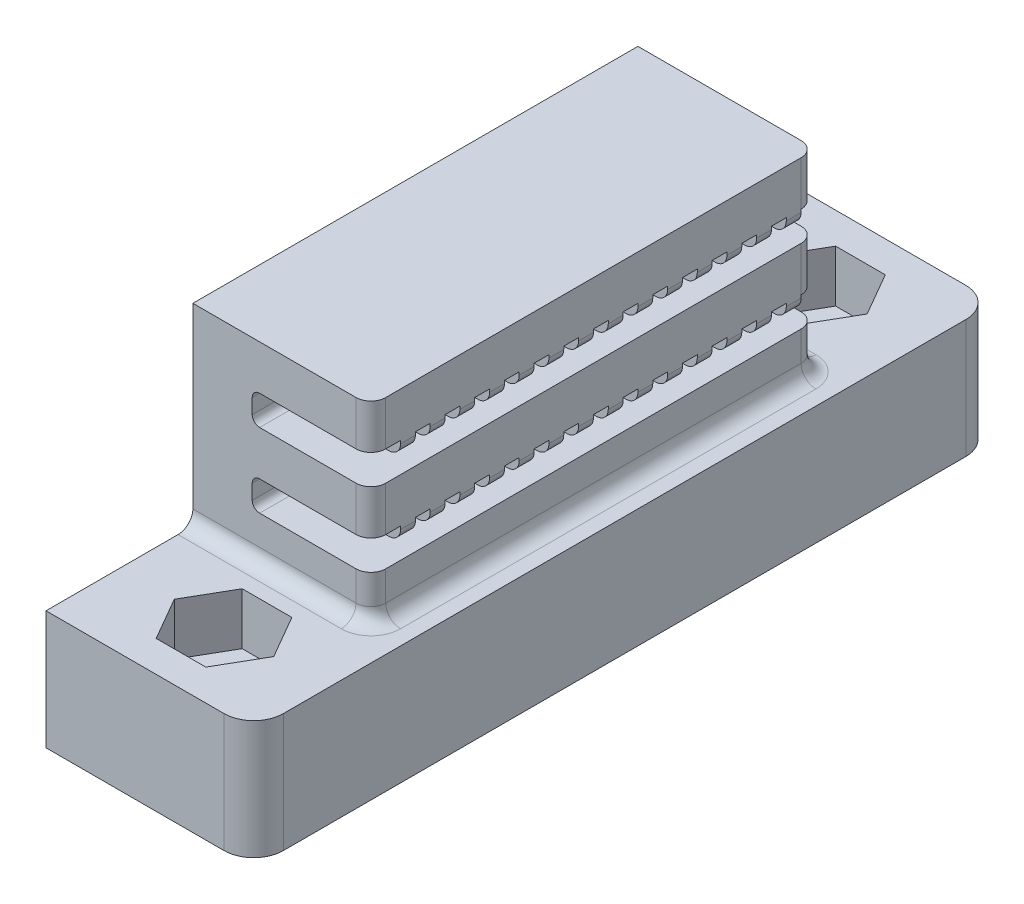
SolidWorks part; units mm, degrees
ref_plane "Alzado" through (0, 0, 0) normal (0, 0, 1) x (1, 0, 0)
ref_plane "Planta" through (0, 0, 0) normal (0, 1, 0) x (1, 0, 0)
ref_plane "Vista lateral" through (0, 0, 0) normal (1, 0, 0) x (0, 0, -1)
sketch "Croquis1" plane through (0, 0, 0) normal (0, 1, 0) x (1, 0, 0)
  line L0 (0, 25) -> (14, 25) construction
  line L1 (0, 0) -> (14, 0)
  line L2 (0, 0) -> (0, 50)
  line L3 (0, 50) -> (14, 50)
  line L4 (14, 0) -> (14, 50)
  line L5 (7, 50) -> (7, 0) construction
  circle A0 centre (7, 45) radius 1.55
  circle A1 centre (7, 5) radius 1.55
  dimension "D3" = 3.1
  dimension "D1" = 50
  dimension "D2" = 14
  dimension "D4" = 20
extrude "Saliente-Extruir1" add sketch "Croquis1" along normal blind 8
sketch "Croquis2" plane through (0, 8, 0) normal (0, 1, 0) x (1, 0, 0)
  line L1 (10.3486, 45) -> (8.6743, 47.9)
  line L2 (8.6743, 47.9) -> (5.3257, 47.9)
  line L3 (5.3257, 47.9) -> (3.6514, 45)
  line L4 (3.6514, 45) -> (5.3257, 42.1)
  line L5 (5.3257, 42.1) -> (8.6743, 42.1)
  line L6 (8.6743, 42.1) -> (10.3486, 45)
  line L7 (10.3486, 5) -> (8.6743, 7.9)
  line L8 (8.6743, 7.9) -> (5.3257, 7.9)
  line L9 (5.3257, 7.9) -> (3.6514, 5)
  line L10 (3.6514, 5) -> (5.3257, 2.1)
  line L11 (5.3257, 2.1) -> (8.6743, 2.1)
  line L12 (8.6743, 2.1) -> (10.3486, 5)
  circle A2 centre (7, 45) radius 2.9 construction
  circle A3 centre (7, 5) radius 2.9 construction
  dimension "D1" = 5.8
  dimension "D2" = 5.8
extrude "Cortar-Extruir1" cut sketch "Croquis2" against normal blind 3.5
sketch "Croquis3" plane through (0, 8, 0) normal (0, 1, 0) x (1, 0, 0)
  line L0 (0, 50) -> (0, 0) construction
  line L1 (0, 39.9) -> (14, 39.9)
  line L2 (0, 39.9) -> (0, 9.9)
  line L3 (0, 9.9) -> (14, 9.9)
  line L4 (14, 39.9) -> (14, 9.9)
  line L5 (14, 0) -> (14, 50) construction
  line L6 (5.3257, 42.1) -> (8.6743, 42.1) construction
  dimension "D1" = 30
  dimension "D2" = 2.2
extrude "Saliente-Extruir3" add sketch "Croquis3" along normal blind 13
sketch "Croquis4" plane through (14, 0, 0) normal (1, 0, 0) x (0, 0, -1)
  line L0 (39.9, 21) -> (39.9, 8) construction
  line L1 (39.9, 18) -> (38.9, 18)
  line L2 (39.9, 18) -> (39.9, 16)
  line L3 (39.9, 16) -> (9.9, 16)
  line L4 (9.9, 18) -> (9.9, 16)
  line L5 (9.9, 21) -> (9.9, 8) construction
  line L6 (39.9, 8) -> (50, 8) construction
  line L7 (39.9, 13) -> (38.9, 13)
  line L8 (39.9, 13) -> (39.9, 11)
  line L9 (39.9, 11) -> (9.9, 11)
  line L10 (9.9, 13) -> (9.9, 11)
  line L11 (36.9, 18) -> (36.9, 17)
  line L13 (38.9, 18) -> (38.9, 17)
  line L14 (38.9, 17) -> (37.9, 17)
  line L15 (37.9, 18) -> (37.9, 17)
  line L16 (36.9, 17) -> (35.9, 17)
  line L17 (35.9, 18) -> (35.9, 17)
  line L18 (34.9, 18) -> (34.9, 17)
  line L19 (34.9, 17) -> (33.9, 17)
  line L20 (33.9, 18) -> (33.9, 17)
  line L21 (32.9, 18) -> (32.9, 17)
  line L22 (32.9, 17) -> (31.9, 17)
  line L23 (31.9, 18) -> (31.9, 17)
  line L24 (30.9, 18) -> (30.9, 17)
  line L25 (30.9, 17) -> (29.9, 17)
  line L26 (29.9, 18) -> (29.9, 17)
  line L27 (28.9, 18) -> (28.9, 17)
  line L28 (28.9, 17) -> (27.9, 17)
  line L29 (27.9, 18) -> (27.9, 17)
  line L30 (26.9, 18) -> (26.9, 17)
  line L31 (26.9, 17) -> (25.9, 17)
  line L32 (25.9, 18) -> (25.9, 17)
  line L33 (24.9, 18) -> (24.9, 17)
  line L34 (24.9, 17) -> (23.9, 17)
  line L35 (23.9, 18) -> (23.9, 17)
  line L36 (22.9, 18) -> (22.9, 17)
  line L37 (22.9, 17) -> (21.9, 17)
  line L38 (21.9, 18) -> (21.9, 17)
  line L39 (20.9, 18) -> (20.9, 17)
  line L40 (20.9, 17) -> (19.9, 17)
  line L41 (19.9, 18) -> (19.9, 17)
  line L42 (18.9, 18) -> (18.9, 17)
  line L43 (18.9, 17) -> (17.9, 17)
  line L44 (17.9, 18) -> (17.9, 17)
  line L45 (16.9, 18) -> (16.9, 17)
  line L46 (16.9, 17) -> (15.9, 17)
  line L47 (15.9, 18) -> (15.9, 17)
  line L48 (14.9, 18) -> (14.9, 17)
  line L49 (14.9, 17) -> (13.9, 17)
  line L50 (13.9, 18) -> (13.9, 17)
  line L51 (12.9, 18) -> (12.9, 17)
  line L52 (12.9, 17) -> (11.9, 17)
  line L53 (11.9, 18) -> (11.9, 17)
  line L54 (38.9, 18) -> (36.9, 18) construction
  line L55 (36.9, 13) -> (36.9, 12)
  line L57 (38.9, 13) -> (38.9, 12)
  line L58 (38.9, 12) -> (37.9, 12)
  line L59 (37.9, 13) -> (37.9, 12)
  line L60 (36.9, 12) -> (35.9, 12)
  line L61 (35.9, 13) -> (35.9, 12)
  line L62 (34.9, 13) -> (34.9, 12)
  line L63 (34.9, 12) -> (33.9, 12)
  line L64 (33.9, 13) -> (33.9, 12)
  line L65 (32.9, 13) -> (32.9, 12)
  line L66 (32.9, 12) -> (31.9, 12)
  line L67 (31.9, 13) -> (31.9, 12)
  line L68 (30.9, 13) -> (30.9, 12)
  line L69 (30.9, 12) -> (29.9, 12)
  line L70 (29.9, 13) -> (29.9, 12)
  line L71 (28.9, 13) -> (28.9, 12)
  line L72 (28.9, 12) -> (27.9, 12)
  line L73 (27.9, 13) -> (27.9, 12)
  line L74 (26.9, 13) -> (26.9, 12)
  line L75 (26.9, 12) -> (25.9, 12)
  line L76 (25.9, 13) -> (25.9, 12)
  line L77 (24.9, 13) -> (24.9, 12)
  line L78 (24.9, 12) -> (23.9, 12)
  line L79 (23.9, 13) -> (23.9, 12)
  line L80 (22.9, 13) -> (22.9, 12)
  line L81 (22.9, 12) -> (21.9, 12)
  line L82 (21.9, 13) -> (21.9, 12)
  line L83 (20.9, 13) -> (20.9, 12)
  line L84 (20.9, 12) -> (19.9, 12)
  line L85 (19.9, 13) -> (19.9, 12)
  line L86 (18.9, 13) -> (18.9, 12)
  line L87 (18.9, 12) -> (17.9, 12)
  line L88 (17.9, 13) -> (17.9, 12)
  line L89 (16.9, 13) -> (16.9, 12)
  line L90 (16.9, 12) -> (15.9, 12)
  line L91 (15.9, 13) -> (15.9, 12)
  line L92 (14.9, 13) -> (14.9, 12)
  line L93 (14.9, 12) -> (13.9, 12)
  line L94 (13.9, 13) -> (13.9, 12)
  line L95 (12.9, 13) -> (12.9, 12)
  line L96 (12.9, 12) -> (11.9, 12)
  line L97 (11.9, 13) -> (11.9, 12)
  line L98 (38.9, 13) -> (36.9, 13) construction
  line L99 (37.9, 18) -> (36.9, 18)
  line L100 (35.9, 18) -> (34.9, 18)
  line L101 (33.9, 18) -> (32.9, 18)
  line L102 (31.9, 18) -> (30.9, 18)
  line L103 (29.9, 18) -> (28.9, 18)
  line L104 (27.9, 18) -> (26.9, 18)
  line L105 (25.9, 18) -> (24.9, 18)
  line L106 (23.9, 18) -> (22.9, 18)
  line L107 (21.9, 18) -> (20.9, 18)
  line L108 (19.9, 18) -> (18.9, 18)
  line L109 (17.9, 18) -> (16.9, 18)
  line L110 (15.9, 18) -> (14.9, 18)
  line L111 (13.9, 18) -> (12.9, 18)
  line L112 (11.9, 18) -> (9.9, 18)
  line L113 (37.9, 13) -> (36.9, 13)
  line L114 (35.9, 13) -> (34.9, 13)
  line L115 (33.9, 13) -> (32.9, 13)
  line L116 (31.9, 13) -> (30.9, 13)
  line L117 (29.9, 13) -> (28.9, 13)
  line L118 (27.9, 13) -> (26.9, 13)
  line L119 (25.9, 13) -> (24.9, 13)
  line L120 (23.9, 13) -> (22.9, 13)
  line L121 (21.9, 13) -> (20.9, 13)
  line L122 (19.9, 13) -> (18.9, 13)
  line L123 (17.9, 13) -> (16.9, 13)
  line L124 (15.9, 13) -> (14.9, 13)
  line L125 (13.9, 13) -> (12.9, 13)
  line L126 (11.9, 13) -> (9.9, 13)
  dimension "D1" = 2
  dimension "D2" = 2
  dimension "D3" = 3
  dimension "D4" = 3
  dimension "D5" = 1
  dimension "D6" = 1
  dimension "D7" = 1
  dimension "D9" = 2
  dimension "D10" = 1
  dimension "D11" = 1
  dimension "D12" = 1
  dimension "D14" = 2
  dimension "D8" = 14
  dimension "D13" = 14
extrude "Cortar-Extruir2" cut sketch "Croquis4" against normal blind 10
sketch "Croquis5" plane through (14, 0, 0) normal (1, 0, 0) x (0, 0, -1)
  line L1 (39.9, 8) -> (9.9, 8)
  line L2 (39.9, 8) -> (39.9, 21)
  line L3 (39.9, 21) -> (9.9, 21)
  line L4 (9.9, 8) -> (9.9, 21)
extrude "Cortar-Extruir3" cut sketch "Croquis5" against normal blind 2
fillet "Redondeo1" radius 0.8 28 edges at (12, 12, -12.4) (12, 12, -14.4) (12, 12, -16.4) (12, 12, -18.4) (12, 12, -20.4) (12, 12, -22.4) (12, 12, -24.4) (12, 12, -26.4) (12, 12, -28.4) (12, 12, -30.4) (12, 12, -32.4) (12, 12, -34.4) (12, 12, -36.4) (12, 12, -38.4) (12, 17, -38.4) (12, 17, -36.4) (12, 17, -34.4) (12, 17, -32.4) (12, 17, -30.4) (12, 17, -28.4) (12, 17, -26.4) (12, 17, -24.4) (12, 17, -22.4) (12, 17, -20.4) (12, 17, -18.4) (12, 17, -16.4) (12, 17, -14.4) (12, 17, -12.4)
fillet "Redondeo2" radius 2 2 edges at (14, 4, -50) (14, 4, 0)
fillet "Redondeo3" radius 1 6 edges at (12, 19.5, -39.9) (12, 14.5, -39.9) (12, 9.5, -39.9) (12, 9.5, -9.9) (12, 14.5, -9.9) (12, 19.5, -9.9)
fillet "Redondeo4" radius 1 5 edges at (5.5, 8, -9.9) (11.7071, 8, -10.1929) (12, 8, -24.9) (11.7071, 8, -39.6071) (5.5, 8, -39.9)
fillet "Redondeo5" radius 0.5 32 edges at (4, 13, -10.9) (4, 13, -13.4) (4, 13, -15.4) (4, 13, -17.4) (4, 13, -19.4) (4, 13, -21.4) (4, 13, -25.4) (4, 13, -23.4) (4, 13, -27.4) (4, 13, -29.4) (4, 13, -31.4) (4, 13, -33.4) (4, 13, -35.4) (4, 13, -37.4) (4, 13, -39.4) (4, 18, -39.4) (4, 18, -37.4) (4, 18, -35.4) (4, 18, -33.4) (4, 18, -31.4) (4, 18, -29.4) (4, 18, -27.4) (4, 18, -25.4) (4, 18, -23.4) (4, 18, -21.4) (4, 18, -19.4) (4, 18, -17.4) (4, 18, -15.4) (4, 18, -13.4) (4, 18, -10.9) (4, 16, -24.9) (4, 11, -24.9)
